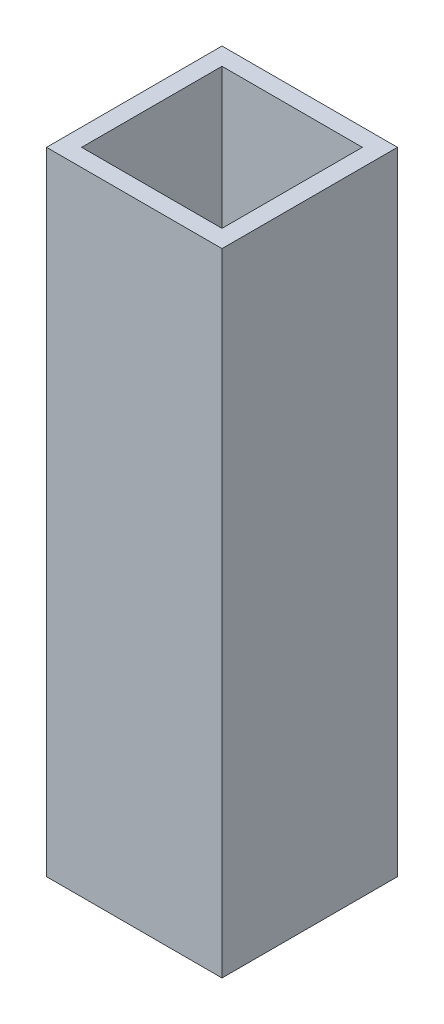
SolidWorks part; units mm, degrees
ref_plane "Front Plane" through (0, 0, 0) normal (0, 0, 1) x (1, 0, 0)
ref_plane "Top Plane" through (0, 0, 0) normal (0, 1, 0) x (1, 0, 0)
ref_plane "Right Plane" through (0, 0, 0) normal (1, 0, 0) x (0, 0, -1)
sketch "Sketch1" plane through (0, 0, 0) normal (0, 1, 0) x (1, 0, 0)
  line L1 (-8.0097, 9.1626) -> (4.4903, 9.1626)
  line L2 (-8.0097, 9.1626) -> (-8.0097, -3.3374)
  line L3 (-8.0097, -3.3374) -> (4.4903, -3.3374)
  line L4 (4.4903, 9.1626) -> (4.4903, -3.3374)
  dimension "D1" = 12.5
  dimension "D2" = 12.5
extrude "Boss-Extrude1" add sketch "Sketch1" along normal blind 45
sketch "Sketch2" plane through (0, 45, 0) normal (0, 1, 0) x (1, 0, 0)
  line L0 (4.4903, 9.1626) -> (-8.0097, 9.1626) construction
  line L1 (-6.7597, 7.9126) -> (3.2403, 7.9126)
  line L2 (-6.7597, 7.9126) -> (-6.7597, -2.0874)
  line L3 (-6.7597, -2.0874) -> (3.2403, -2.0874)
  line L4 (3.2403, 7.9126) -> (3.2403, -2.0874)
  line L5 (4.4903, -3.3374) -> (4.4903, 9.1626) construction
  point P6 (-1.7597, 9.1626)
  dimension "D1" = 10
  dimension "D2" = 10
  dimension "D3" = 1.25
  dimension "D4" = 1.25
extrude "Cut-Extrude1" cut sketch "Sketch2" against normal blind 42.5
